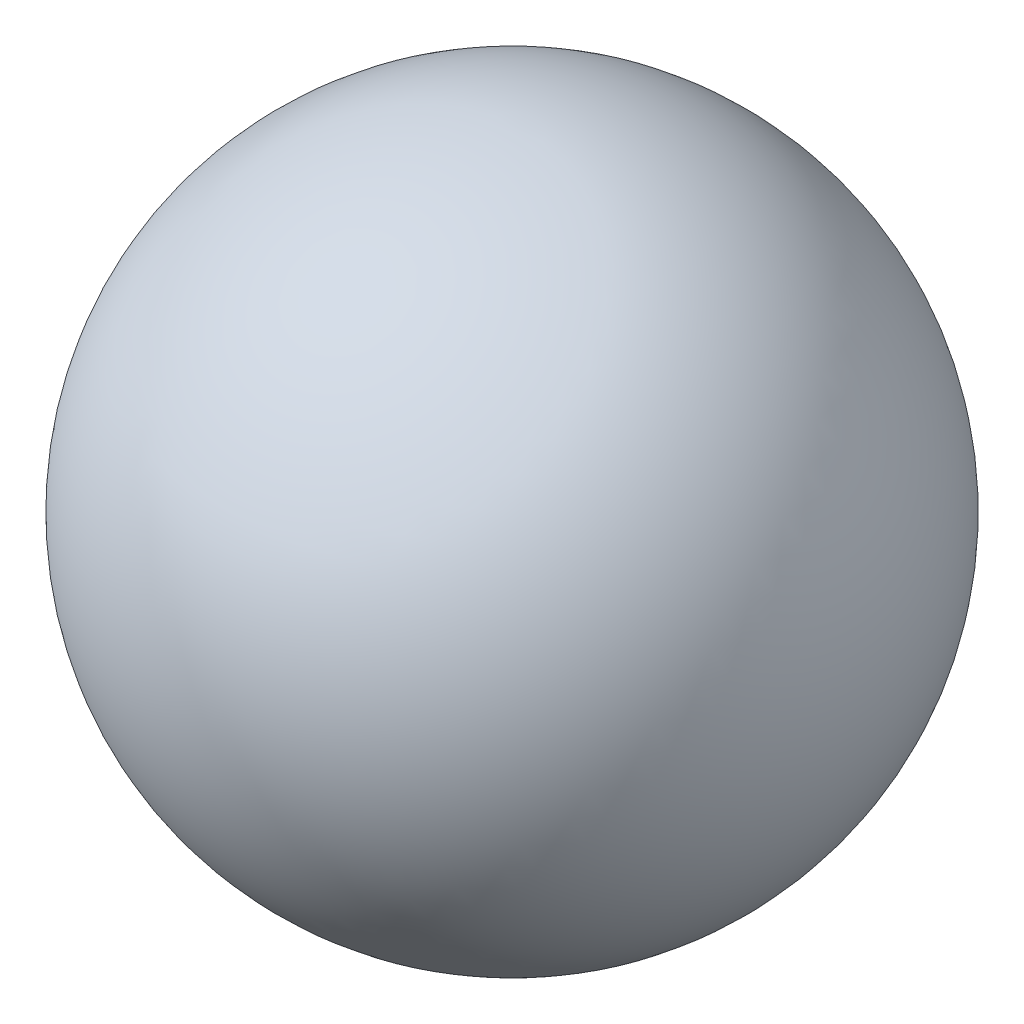
SolidWorks part; units mm, degrees
ref_plane "Front" through (0, 0, 0) normal (0, 0, 1) x (1, 0, 0)
ref_plane "Top" through (0, 0, 0) normal (0, 1, 0) x (1, 0, 0)
ref_plane "Right" through (0, 0, 0) normal (1, 0, 0) x (0, 0, -1)
sketch "Sketch1" plane through (0, 0, 0) normal (0, 0, 1) x (1, 0, 0)
  line L0 (0, 1) -> (0, -1) construction
  line L1 (0, 1) -> (0, -1)
  circle A0 centre (0, 0) radius 1 construction
  arc A1 (0, -1) -> (0, 1) centre (0, 0) ccw
  dimension "D1" = 2
revolve "Revolve1" add sketch "Sketch1" angle 360 about L0
